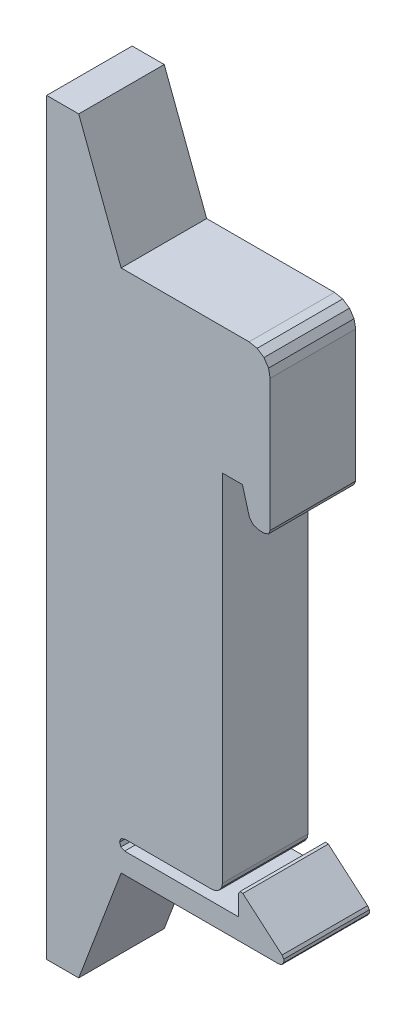
SolidWorks part; units mm, degrees
ref_plane "Front Plane" through (0, 0, 0) normal (0, 0, 1) x (1, 0, 0)
ref_plane "Top Plane" through (0, 0, 0) normal (0, 1, 0) x (1, 0, 0)
ref_plane "Right Plane" through (0, 0, 0) normal (1, 0, 0) x (0, 0, -1)
sketch "Model" plane through (0, 0, 0) normal (0, 0, 1) x (1, 0, 0)
  line L0 (17.4134, 34.2219) -> (17.762, 34.3663)
  line L1 (17.762, 34.3663) -> (17.9064, 34.7148)
  line L2 (17.9064, 47.0385) -> (17.7563, 47.7931)
  line L3 (17.7563, 47.7931) -> (17.3289, 48.4328)
  line L4 (17.3289, 48.4328) -> (16.6892, 48.8602)
  line L5 (16.6892, 48.8602) -> (15.9346, 49.0103)
  line L6 (17.9064, 47.0385) -> (17.9064, 34.7148)
  line L7 (13.4487, 38.4331) -> (14.9487, 38.4331)
  line L8 (14.9487, 1.9338) -> (14.9487, 3.8364)
  line L9 (15.3491, 4.0289) -> (15.0884, 4.0586)
  line L10 (15.0884, 4.0586) -> (14.9487, 3.8364)
  line L11 (13.4487, 3.9056) -> (13.4487, 38.4331)
  line L12 (12.4628, 2.9197) -> (12.8466, 2.9972)
  line L13 (12.8466, 2.9972) -> (13.16, 3.2085)
  line L14 (13.16, 3.2085) -> (13.3712, 3.5218)
  line L15 (13.3712, 3.5218) -> (13.4487, 3.9056)
  line L16 (14.9487, 1.9338) -> (4.2974, 1.9338)
  line L17 (4.2974, 1.9338) -> (3.9455, 2.0879)
  line L18 (3.9455, 2.0879) -> (3.8238, 2.4268)
  line L19 (3.8238, 2.4268) -> (3.9389, 2.7657)
  line L20 (3.9389, 2.7657) -> (4.2974, 2.9197)
  line L21 (4.2974, 2.9197) -> (12.4628, 2.9197)
  line L22 (18.7123, 0) -> (0, 0)
  line L23 (0, 0) -> (0, 49.0103)
  line L24 (0, 49.0103) -> (15.9346, 49.0103)
  line L25 (19.0203, 0.8779) -> (15.3491, 4.0289)
  line L26 (18.7123, 0) -> (18.9975, 0.0908)
  line L27 (18.9975, 0.0908) -> (19.1775, 0.3298)
  line L28 (19.1775, 0.3298) -> (19.1862, 0.6289)
  line L29 (19.1862, 0.6289) -> (19.0203, 0.8779)
  line L30 (14.9487, 38.4331) -> (15.975, 34.7831)
  line L31 (16.8647, 34.2219) -> (17.4134, 34.2219)
  line L32 (15.975, 34.7831) -> (16.3388, 34.3739)
  line L33 (16.3388, 34.3739) -> (16.8647, 34.2219)
extrude "Boss-Extrude1" add sketch "Model" along normal blind 8
sketch "Sketch2" plane through (0, 0, 0) normal (-1, 0, 0) x (0, 0, 1)
  line L0 (0, 24.5052) -> (8, 24.5052) construction
  line L1 (0, 49.0103) -> (0, 0) construction
  line L2 (8, 49.0103) -> (8, 0) construction
  line L4 (0, -10.4948) -> (8, -10.4948)
  line L5 (0, -10.4948) -> (0, 59.5052)
  line L6 (0, 59.5052) -> (8, 59.5052)
  line L7 (8, -10.4948) -> (8, 59.5052)
  line L8 (0, -10.4948) -> (8, 59.5052) construction
  line L9 (0, 59.5052) -> (8, -10.4948) construction
  point P6 (4, 24.5052)
  dimension "D1" = 70
extrude "Boss-Extrude2" add sketch "Sketch2" along normal blind 3
sketch "Sketch4" plane through (0, 0, 8) normal (0, 0, 1) x (1, 0, 0)
  line L0 (0, 59.5052) -> (3.9673, 49.0103)
  line L2 (-3, 24.5052) -> (13.4487, 24.5052) construction
  line L3 (-3, -10.4948) -> (-3, 59.5052) construction
  line L4 (13.4487, 3.9056) -> (13.4487, 38.4331) construction
  line L5 (0, 49.0103) -> (0, 59.5052) construction
  line L6 (0, 49.0103) -> (0, 59.5052)
  line L7 (0, 49.0103) -> (3.9673, 49.0103)
  line L8 (0, 0) -> (0, -10.4948)
  line L9 (0, -10.4948) -> (3.9673, 0)
  line L10 (0, 0) -> (3.9673, 0)
  line L11 (15.9346, 49.0103) -> (0, 49.0103) construction
  point P17 (7.9673, 49.0103)
  dimension "D1" = 4
extrude "Boss-Extrude3" add sketch "Sketch4" against normal up to surface (8 mm away) up to face at (11.8762, 18.847, 0)
sketch "Sketch3" plane through (-3, 0, 0) normal (-1, 0, 0) x (0, 0, 1)
  line L0 (8, 24.5052) -> (0, 24.5052) construction
  line L1 (8, -10.4948) -> (8, 59.5052) construction
  line L2 (0, 59.5052) -> (0, -10.4948) construction
  line L3 (4, 59.5052) -> (4, -10.4948) construction
  line L4 (8, 59.5052) -> (0, 59.5052) construction
  line L5 (0, -10.4948) -> (8, -10.4948) construction
  circle A0 centre (4, 49.5552) radius 1.95
  circle A1 centre (4, -0.5448) radius 1.95
  dimension "D1" = 3.9
  dimension "D2" = 8
  dimension "D3" = 54
extrude "Cut-Extrude1" cut sketch "Sketch3" against normal blind 5
sketch "Sketch5" plane through (0, 0, 8) normal (0, 0, 1) x (1, 0, 0)
  line L0 (14.9487, 38.4331) -> (15.975, 34.7831) construction
  line L1 (14.9487, 38.4331) -> (15.314, 37.1338)
  line L2 (13.4487, 38.4331) -> (14.9487, 38.4331) construction
  line L3 (13.4487, 38.4331) -> (14.9487, 38.4331)
  line L4 (15.314, 37.1338) -> (13.4487, 37.1338)
  line L5 (13.4487, 3.9056) -> (13.4487, 38.4331) construction
  line L6 (13.4487, 37.1338) -> (13.4487, 38.4331)
  line L7 (14.9487, 1.9338) -> (4.2974, 1.9338) construction
  dimension "D1" = 35.2
extrude "Boss-Extrude4" add sketch "Sketch5" against normal up to surface (8 mm away) up to face at (12.085, 18.847, 0)
